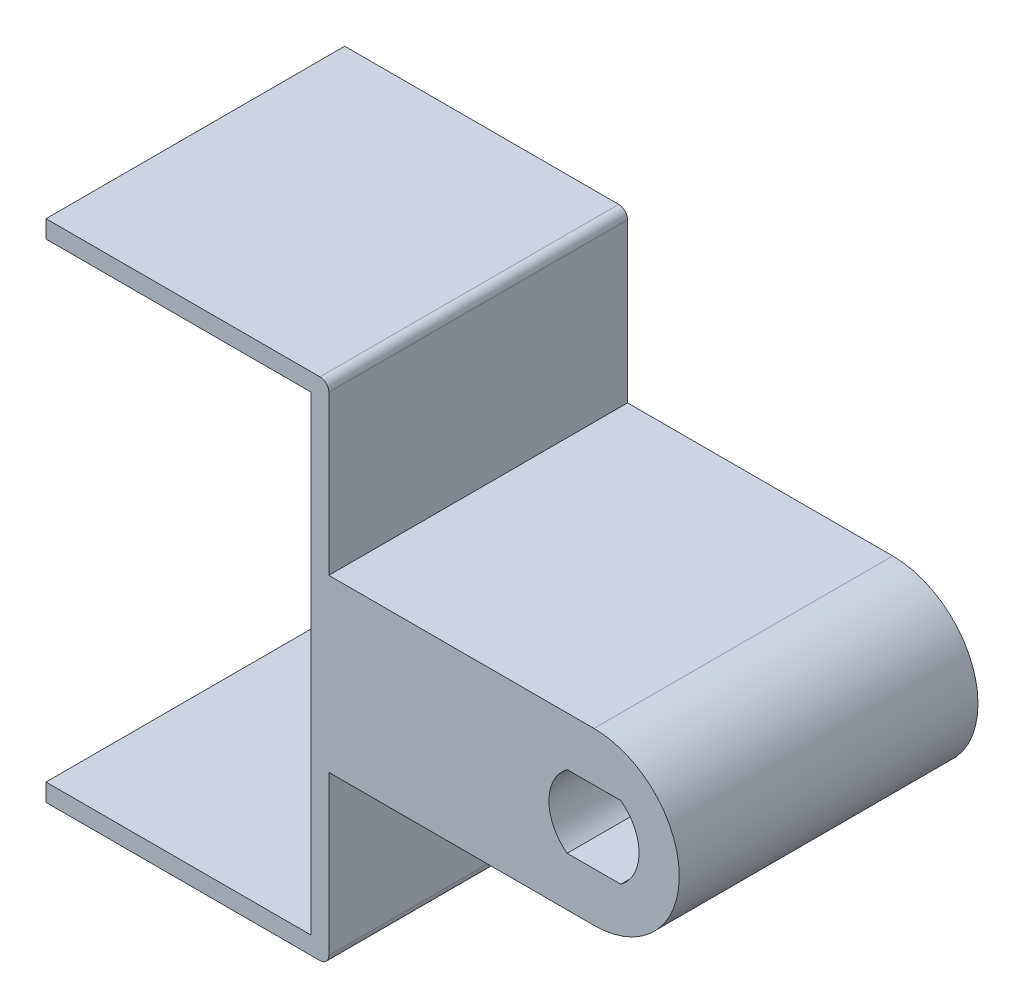
SolidWorks part; units mm, degrees
ref_plane "Front Plane" through (0, 0, 0) normal (0, 0, 1) x (1, 0, 0)
ref_plane "Top Plane" through (0, 0, 0) normal (0, 1, 0) x (1, 0, 0)
ref_plane "Right Plane" through (0, 0, 0) normal (1, 0, 0) x (0, 0, -1)
sketch "Sketch1" plane through (0, 0, 0) normal (0, 0, 1) x (1, 0, 0)
  line L0 (-20, -13.3) -> (20, -13.3)
  line L1 (20, -13.3) -> (20, 13.3)
  line L2 (20, 13.3) -> (-20, 13.3)
  line L3 (-20, -14.3) -> (21, -14.3)
  line L4 (21, -14.3) -> (21, 14.3)
  line L5 (21, 14.3) -> (-20, 14.3)
  line L6 (-20, 14.3) -> (-20, 13.3)
  line L7 (-20, -13.3) -> (-20, -14.3)
  point P8 (0, -13.3)
  point P9 (20, 0)
  dimension "D2" = 26.6
  dimension "D3" = 40
  dimension "D1" = 1
extrude "Boss-Extrude1" add sketch "Sketch1" along normal blind 16.9
sketch "Sketch4" plane through (0, 0, 0) normal (0, 0, -1) x (-1, 0, 0)
  line L0 (-21, 4.825) -> (-36, 4.825)
  line L1 (-21, -14.3) -> (-21, 14.3) construction
  line L3 (-40.391, 2) -> (-30.875, 2)
  line L4 (-30.875, 2) -> (-30.875, -2)
  line L5 (-30.875, -2) -> (-40.391, -2)
  line L7 (-36, -4.825) -> (-21, -4.825)
  line L8 (-21, -4.825) -> (-21, 4.825)
  line L9 (-20, 13.3) -> (-20, -13.3) construction
  arc A0 (-36, -4.825) -> (-40.391, -2) centre (-36, 0) cw
  arc A1 (-36, 4.825) -> (-40.391, 2) centre (-36, 0) ccw
  circle A2 centre (-36, 0) radius 4.825 construction
  point P11 (-30.875, 0)
  point P14 (-21, 0)
  dimension "D3" = 4.825
  dimension "D1" = 4
  dimension "D2" = 9.65
  dimension "D4" = 0.3
  dimension "D5" = 16
extrude "Boss-Extrude2" add sketch "Sketch4" against normal blind 13.5
sketch "Sketch5" plane through (0, 0, 13.5) normal (0, 0, 1) x (1, 0, 0)
  line L6 (21, 4.825) -> (21, -4.825)
  line L7 (21, -4.825) -> (36, -4.825)
  line L8 (40.391, -2) -> (30.875, -2)
  line L9 (30.875, -2) -> (30.875, 2)
  line L10 (30.875, 2) -> (40.391, 2)
  line L11 (36, 4.825) -> (21, 4.825)
  line L12 (21, 4.825) -> (21, -4.825)
  line L13 (21, -4.825) -> (36, -4.825)
  line L17 (36, 4.825) -> (21, 4.825)
  arc A1 (40.391, 2) -> (40.391, -2) centre (36, 0) cw
  arc A2 (36, -4.825) -> (40.391, -2) centre (36, 0) ccw
  arc A3 (40.391, 2) -> (36, 4.825) centre (36, 0) ccw
  arc A4 (36, -4.825) -> (40.391, -2) centre (36, 0) ccw
  arc A5 (40.391, 2) -> (36, 4.825) centre (36, 0) ccw
  dimension "D1" = 0
extrude "Boss-Extrude3" add sketch "Sketch5" along normal up to surface (3.4 mm away) up to face at (0.25, 0, 16.9)
sketch "Sketch8" plane through (0, 0, 0) normal (0, 0, -1) x (-1, 0, 0)
  line L5 (-37.5, 2) -> (-40.391, 2)
  line L6 (-40.391, -2) -> (-37.5, -2)
  line L7 (-34.5, 2) -> (-30.875, 2)
  line L8 (-30.875, 2) -> (-30.875, -2)
  line L9 (-30.875, -2) -> (-34.5, -2)
  arc A2 (-34.5, -2) -> (-34.5, 2) centre (-36, 0) ccw
  arc A3 (-37.5, 2) -> (-37.5, -2) centre (-36, 0) ccw
  arc A4 (-40.391, 2) -> (-40.391, -2) centre (-36, 0) ccw
  point P5 (-40.7205, 0)
  point P14 (-40.391, -2)
  point P16 (-36.1118, 0)
  dimension "D1" = 2.5
  dimension "D2" = 36
extrude "Boss-Extrude4" add sketch "Sketch8" against normal up to surface (13.5 mm away) up to face at (35.7415, 0, 13.5)
sketch "Sketch9" plane through (0, 0, 13.5) normal (0, 0, -1) x (-1, 0, 0)
  line L2 (-37.5, -2) -> (-34.5, -2)
  line L3 (-34.5, 2) -> (-37.5, 2)
  line L4 (-37.5, -2) -> (-34.5, -2)
  line L5 (-34.5, 2) -> (-37.5, 2)
  arc A1 (-34.5, -2) -> (-34.5, 2) centre (-36, 0) ccw
  arc A6 (-34.5, -2) -> (-34.5, 2) centre (-36, 0) ccw
  arc A7 (-37.5, 2) -> (-37.5, -2) centre (-36, 0) ccw
  arc A8 (-37.5, 2) -> (-37.5, -2) centre (-36, 0) ccw
  dimension "D1" = 0
extrude "Cut-Extrude1" cut sketch "Sketch9" against normal through all
chamfer "Chamfer1" distance 2 angle 30 4 edges at (33.5, 0, 0) (38.5, 0, 0) (36, -2, 0) (36, 2, 0)
sketch "Sketch10" plane through (0, 0, 0) normal (0, 0, -1) x (-1, 0, 0)
  line L0 (20, -14.3) -> (-21, -14.3) construction
  line L1 (20, 14.3) -> (-5, 14.3)
  line L2 (20, 14.3) -> (20, -14.3)
  line L3 (20, -14.3) -> (-5, -14.3)
  line L4 (-5, 14.3) -> (-5, -14.3)
  line L5 (-20, 13.3) -> (-20, -13.3) construction
  dimension "D1" = 15
sketch "Sketch11" plane through (0, 0, 0) normal (0, 0, -1) x (-1, 0, 0)
  line L0 (-37.5, -2) -> (-34.5, -2) construction
  line L1 (-34.5, 2) -> (-37.5, 2) construction
  line L2 (-37.5, -2) -> (-34.5, -2) construction
  line L3 (-34.5, 2) -> (-37.5, 2) construction
  line L4 (-34.4834, 2.05) -> (-37.5166, 2.05)
  line L5 (-37.5166, -2.05) -> (-34.4834, -2.05)
  arc A0 (-34.5, -2) -> (-34.5, 2) centre (-36, 0) ccw construction
  arc A1 (-37.5, 2) -> (-37.5, -2) centre (-36, 0) ccw construction
  arc A2 (-34.5, -2) -> (-34.5, 2) centre (-36, 0) ccw construction
  arc A3 (-37.5, 2) -> (-37.5, -2) centre (-36, 0) ccw construction
  arc A4 (-37.5166, 2.05) -> (-37.5166, -2.05) centre (-36, 0) ccw
  arc A5 (-34.4834, -2.05) -> (-34.4834, 2.05) centre (-36, 0) ccw
  dimension "D1" = 0.05
extrude "Cut-Extrude2" cut sketch "Sketch11" against normal through all
fillet "Fillet1" radius 0.5 4 edges at (-20, 14.3, 8.45) (-20, -14.3, 8.45) (21, 14.3, 8.45) (21, -14.3, 8.45)
sketch "Sketch6" plane through (0, 0, 16.9) normal (0, 0, 1) x (1, 0, 0)
  arc A0 (36, -4.825) -> (36, 4.825) centre (36, 0) ccw construction
  arc A1 (36, -4.825) -> (36, 4.825) centre (36, 0) ccw
  circle A2 centre (36, 0) radius 4.8263
extrude "Cut-Extrude3" cut sketch "Sketch10" against normal through all
